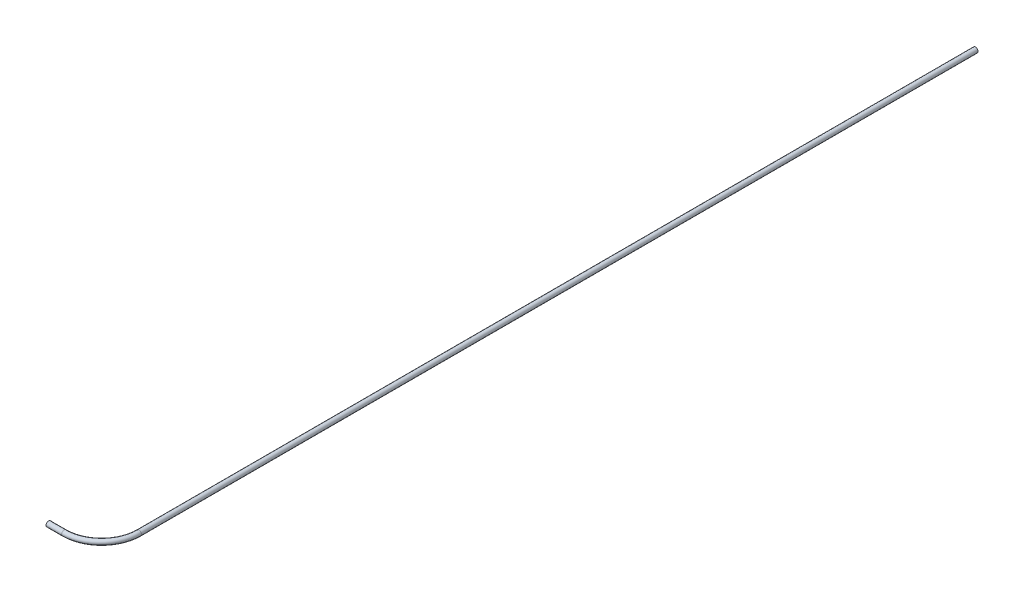
SolidWorks part; units mm, degrees
material "6061-T6 (SS)"
ref_plane "Front Plane" through (0, 0, 0) normal (0, 0, 1) x (1, 0, 0)
ref_plane "Top Plane" through (0, 0, 0) normal (0, 1, 0) x (1, 0, 0)
ref_plane "Right Plane" through (0, 0, 0) normal (1, 0, 0) x (0, 0, -1)
sketch "Sketch1" plane through (0, 0, 0) normal (0, 1, 0) x (1, 0, 0)
  line L0 (49.5217, 34.925) -> (49.5217, 815.975)
  line L1 (49.5217, 34.925) -> (14.5967, 34.925) construction
  line L2 (14.5967, 34.925) -> (14.5967, 0) construction
  line L3 (14.5967, 0) -> (0, 0)
  arc A0 (14.5967, 0) -> (49.5217, 34.925) centre (14.5967, 34.925) ccw
  dimension "D2" = 34.925
  dimension "D3" = 14.5967
  dimension "D1" = 781.05
sketch "Sketch2" plane through (0, 0, 0) normal (1, 0, 0) x (0, 0, -1)
  circle A0 centre (0, 0) radius 2.3813
  circle A1 centre (0, 0) radius 1.8225
  dimension "D1" = 4.7625
  dimension "D2" = 0.5588
sweep "Sweep1" add profiles "Sketch2" path "Sketch1"
